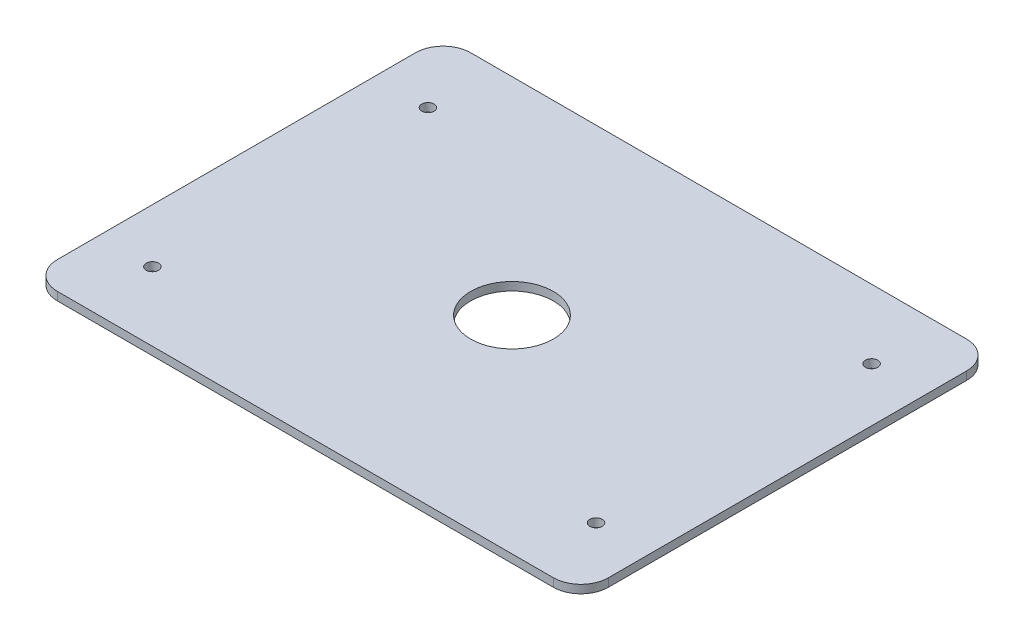
SolidWorks part; units mm, degrees
material "Cedar"
ref_plane "Front Plane" through (0, 0, 0) normal (0, 0, 1) x (1, 0, 0)
ref_plane "Top Plane" through (0, 0, 0) normal (0, 1, 0) x (1, 0, 0)
ref_plane "Right Plane" through (0, 0, 0) normal (1, 0, 0) x (0, 0, -1)
sketch "Sketch1" plane through (0, 0, 0) normal (0, 1, 0) x (1, 0, 0)
  line L0 (111.1, 83.14) -> (111.1, 84.07)
  line L1 (0, 0) -> (111.1, 0)
  line L2 (0, 0) -> (0, 83.14)
  line L3 (0, 83.14) -> (111.1, 83.14)
  line L4 (111.1, 0) -> (111.1, 83.14)
  line L5 (111.1, 0) -> (111.1, -0.93)
  line L6 (111.1, -0.93) -> (167.2, -0.93)
  line L7 (167.2, -0.93) -> (167.2, 84.07)
  line L8 (167.2, 84.07) -> (111.1, 84.07)
  line L9 (169.2, 97.57) -> (-78.8, 97.57)
  line L10 (169.2, -3.43) -> (-78.8, -3.43)
  line L11 (169.2, -14.43) -> (169.2, 97.57)
  line L12 (169.2, 86.57) -> (-78.8, 86.57)
  line L13 (-78.8, -14.43) -> (-78.8, 97.57)
  line L14 (169.2, -14.43) -> (-78.8, -14.43)
  line L16 (-114.8, 103.57) -> (205.2, 103.57)
  line L17 (-114.8, 103.57) -> (-114.8, -216.43)
  line L18 (-114.8, -216.43) -> (205.2, -216.43)
  line L19 (205.2, 103.57) -> (205.2, -216.43)
  line L20 (-54.8, -60.43) -> (145.2, -60.43)
  line L21 (-54.8, -60.43) -> (-54.8, -210.43)
  line L22 (-54.8, -210.43) -> (145.2, -210.43)
  line L23 (145.2, -60.43) -> (145.2, -210.43)
  circle A0 centre (101.6, 16) radius 1.65
  circle A1 centre (2.15, 2.15) radius 1.65
  circle A2 centre (33.15, 2.15) radius 1.65
  circle A3 centre (2.15, 53.15) radius 1.65
  circle A4 centre (57.1, 76.14) radius 1.65
  circle A5 centre (163.7, 2.57) radius 1.35
  circle A6 centre (114.7, 2.57) radius 1.35
  circle A7 centre (163.7, 60.57) radius 1.35
  circle A8 centre (114.7, 60.57) radius 1.35
  circle A9 centre (-14.3, -8.93) radius 1.65
  circle A10 centre (-66.8, -8.93) radius 1.65
  circle A11 centre (-14.3, 92.07) radius 1.65
  circle A12 centre (-66.8, 92.07) radius 1.65
  circle A13 centre (-35.3, -85.43) radius 2.25
  circle A14 centre (125.7, -85.43) radius 2.25
  circle A15 centre (125.7, -185.43) radius 2.25
  circle A16 centre (-35.3, -185.43) radius 2.25
  circle A17 centre (45.2, -135.43) radius 15
  dimension "D6" = 3.3
  dimension "D9" = 3.3
  dimension "D10" = 2
  dimension "D12" = 3.3
  dimension "D14" = 3.3
  dimension "D16" = 3.3
  dimension "D17" = 54
  dimension "D18" = 7
  dimension "D19" = 2.7
  dimension "D20" = 3.5
  dimension "D21" = 3.5
  dimension "D22" = 2.7
  dimension "D23" = 3.5
  dimension "D25" = 2.7
  dimension "D26" = 58
  dimension "D28" = 2.7
  dimension "D36" = 11
  dimension "D37" = 320
  dimension "D38" = 248
  dimension "D39" = 6
  dimension "D40" = 320
  dimension "D41" = 150
  dimension "D44" = 200
  dimension "D46" = 100
  dimension "D30" = 2
  dimension "D35" = 11
  dimension "D33" = 12
  dimension "D34" = 8
  dimension "D47" = 25
  dimension "D49" = 161
  dimension "D52" = 19.5
  dimension "D53" = 100
  dimension "D54" = 75
  dimension "D55" = 19.5
  dimension "D1" = 111.1
  dimension "D2" = 83.14
  dimension "D3" = 0.93
  dimension "D4" = 0.93
  dimension "D5" = 56.1
  dimension "D7" = 9.5
  dimension "D8" = 16
  dimension "D11" = 2.15
  dimension "D13" = 31
  dimension "D15" = 51
  dimension "D24" = 3.6
  dimension "D27" = 58
  dimension "D29" = 2
  dimension "D31" = 90
  dimension "D32" = 2.5
  dimension "D42" = 6
  dimension "D43" = 36
  dimension "D45" = 60
  dimension "D48" = 0
  dimension "D50" = 161
  dimension "D51" = 0
extrude "Boss-Extrude1" add sketch "Sketch1" along normal blind 3 contours L23 L20 L21 L22 A17 A16 A15 A14 A13 | L12 L13 L10 L11
fillet "Fillet1" radius 10 4 edges at (-54.8, 1.5, 60.43) (145.2, 1.5, 60.43) (145.2, 1.5, 210.43) (-54.8, 1.5, 210.43)
